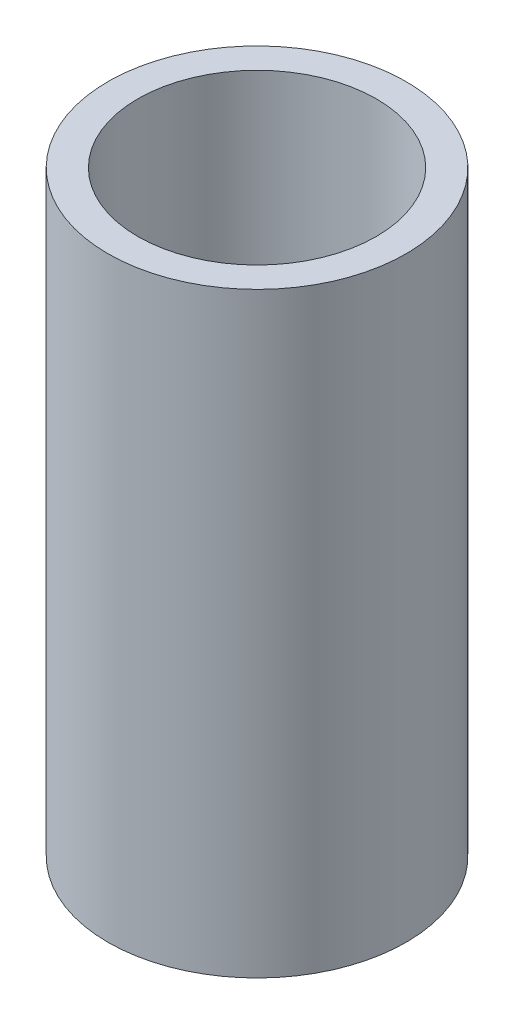
SolidWorks part; units mm, degrees
ref_plane "Front Plane" through (0, 0, 0) normal (0, 0, 1) x (1, 0, 0)
ref_plane "Top Plane" through (0, 0, 0) normal (0, 1, 0) x (1, 0, 0)
ref_plane "Right Plane" through (0, 0, 0) normal (1, 0, 0) x (0, 0, -1)
sketch "Sketch1" plane through (0, 0, 0) normal (0, 1, 0) x (1, 0, 0)
  circle A0 centre (0, 0) radius 2
  circle A1 centre (0, 0) radius 1.6
  dimension "D1" = 4
  dimension "D2" = 3.2
extrude "Boss-Extrude1" add sketch "Sketch1" along normal blind 8
